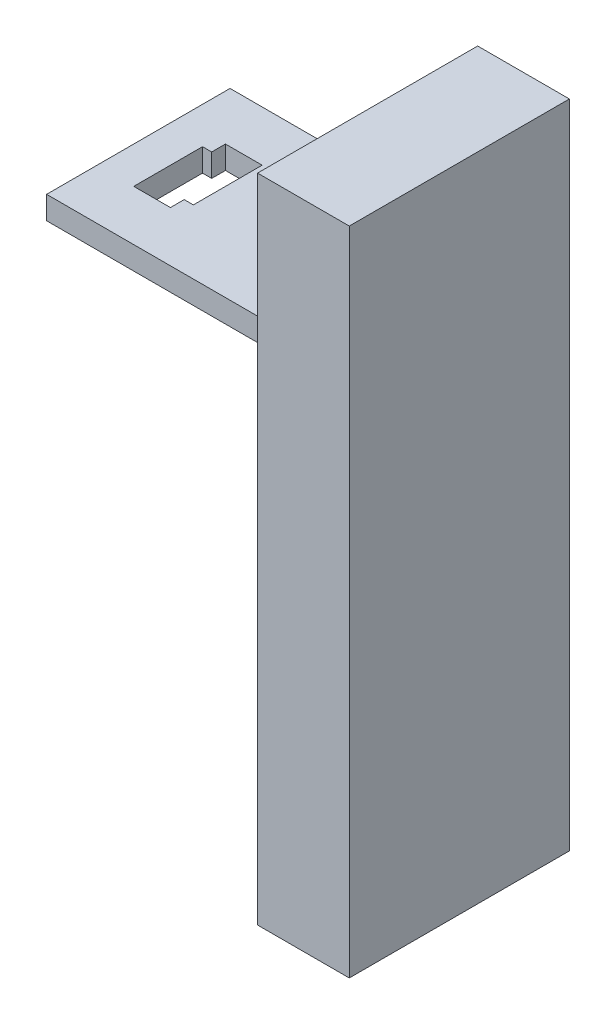
SolidWorks part; units mm, degrees
ref_plane "Front Plane" through (0, 0, 0) normal (1, 0, 0) x (0, 1, 0)
ref_plane "Top Plane" through (0, 0, 0) normal (0, 0, 1) x (0, 1, 0)
ref_plane "Right Plane" through (0, 0, 0) normal (0, 1, 0) x (-1, 0, 0)
sketch "Sketch2" plane through (0, 0, 0) normal (1, 0, 0) x (0, 1, 0)
  line L0 (45.5, 24) -> (18.7, 24) construction
  line L1 (-31.5, 24) -> (110.5095, 24)
  line L2 (-31.5, 24) -> (-31.5, -24)
  line L3 (-31.5, -24) -> (110.5095, -24)
  line L4 (110.5095, 24) -> (110.5095, -24)
  line L5 (-31.5, 24) -> (110.5095, -24) construction
  line L6 (-31.5, -24) -> (110.5095, 24) construction
  line L11 (-31.5, 6) -> (-31.5, -6) construction
  point P0 (6.1229, -11.2832)
  dimension "D1" = 0
  dimension "D2" = 0
extrude "Boss-Extrude1" add sketch "Sketch2" along normal blind 20
sketch "Sketch3" plane through (0, 0, 0) normal (-1, 0, 0) x (0, -1, 0)
  circle A0 centre (-14, 13) radius 2.6
  circle A1 centre (13.9762, 13) radius 2.6
  circle A2 centre (13.9762, -13) radius 2.6
  circle A3 centre (-14, -13) radius 2.6
  point P0 (13.9762, 13)
  point P1 (13.9762, -13)
  point P2 (-14, -13)
  point P3 (-14, 13)
  dimension "D1" = 5.2
  dimension "D2" = 5.2
  dimension "D3" = 5.2
  dimension "D4" = 5.2
extrude "Cut-Extrude1" cut sketch "Sketch3" against normal blind 16
sketch "Sketch4" plane through (0, 0, 0) normal (-1, 0, 0) x (0, -1, 0)
  line L0 (-65.5, 5) -> (-65.5, -5) construction
  line L1 (-74.5, 20) -> (-79.5, 20)
  line L2 (-74.5, 20) -> (-74.5, -20)
  line L3 (-74.5, -20) -> (-79.5, -20)
  line L4 (-79.5, 20) -> (-79.5, -20)
  line L5 (-74.5, 20) -> (-79.5, -20) construction
  line L6 (-74.5, -20) -> (-79.5, 20) construction
  line L7 (-110.5095, 24) -> (31.5, 24) construction
  line L8 (31.5, -24) -> (-110.5095, -24) construction
  point P0 (-77, 0)
  dimension "D1" = 9
  dimension "D2" = 40
  dimension "D3" = 0
  dimension "D4" = 48
  dimension "D5" = 5
extrude "Boss-Extrude2" add sketch "Sketch4" along normal blind 50 and the other way blind 2
sketch "Sketch5" plane through (0, 79.5, 0) normal (0, 1, 0) x (-1, 0, 0)
  line L0 (40, -9) -> (40, -6)
  line L5 (32, 9) -> (42, 9)
  line L6 (32, 9) -> (32, -9)
  line L7 (32, -9) -> (42, -9)
  line L8 (42, 9) -> (42, -9)
  line L9 (32, 9) -> (42, -9) construction
  line L10 (32, -9) -> (42, 9) construction
  line L11 (40, -6) -> (42, -6)
  line L12 (42, -6) -> (42, -9)
  line L13 (34, 9) -> (34, 6)
  line L14 (34, 6) -> (32, 6)
  point P0 (37, 0)
  point P1 (37, 0)
  dimension "D1" = 18
  dimension "D2" = 10
  dimension "D3" = 3
  dimension "D4" = 2
  dimension "D5" = 3
  dimension "D6" = 2
extrude "Cut-Extrude2" cut sketch "Sketch5" against normal up to surface (5 mm away) contours L13 L14 L6 L7 L0 L11 L8 L5 up to face at (-25, 74.5, 0)
ref_plane "Plane1" through (0, 0, 0) normal (-1, 0, 0) x (0, 0, 1)
split "Split1" trim tools "Plane1" bodies to split 106 resulting bodies 107 108
sketch "Sketch8" plane through (0, 0, 0) normal (-1, 0, 0) x (0, -1, 0)
  line L1 (-74.6, 20.5) -> (-79.8, 20.5)
  line L2 (-74.6, 20.5) -> (-74.6, -20.5)
  line L3 (-74.6, -20.5) -> (-79.8, -20.5)
  line L4 (-79.8, 20.5) -> (-79.8, -20.5)
  line L5 (-74.6, 20.5) -> (-79.8, -20.5) construction
  line L6 (-74.6, -20.5) -> (-79.8, 20.5) construction
  point P0 (-77.2, 0)
  dimension "D1" = 5.2
  dimension "D2" = 41
  dimension "D3" = 11.7
  dimension "D4" = 0
extrude "Cut-Extrude3" cut sketch "Sketch8" against normal blind 2
